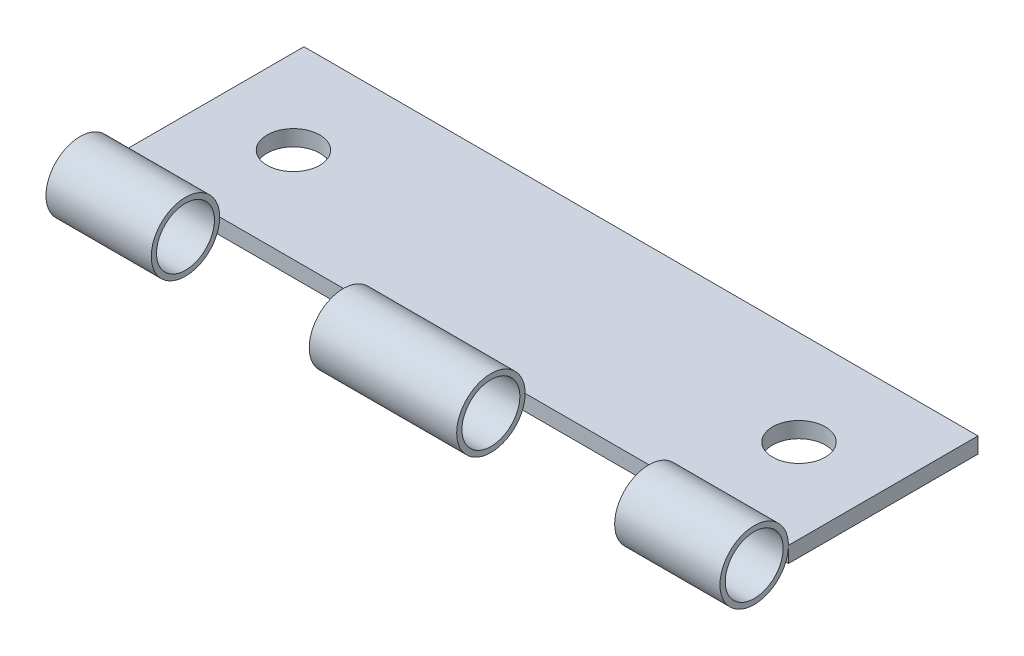
SolidWorks part; units mm, degrees
ref_plane "Front Plane" through (0, 0, 0) normal (0, 0, 1) x (1, 0, 0)
ref_plane "Top Plane" through (0, 0, 0) normal (0, 1, 0) x (1, 0, 0)
ref_plane "Right Plane" through (0, 0, 0) normal (1, 0, 0) x (0, 0, -1)
sketch "Sketch1" plane through (0, 0, 0) normal (0, 1, 0) x (1, 0, 0)
  line L1 (-32, 9) -> (32, 9)
  line L2 (-32, 9) -> (-32, -9)
  line L3 (-32, -9) -> (32, -9)
  line L4 (32, 9) -> (32, -9)
  line L5 (-32, 9) -> (32, -9) construction
  line L6 (-32, -9) -> (32, 9) construction
  point P0 (0, 0)
  dimension "D1" = 64
  dimension "D2" = 18
extrude "Boss-Extrude1" add sketch "Sketch1" along normal blind 1.5
sketch "Sketch2" plane through (0, 0, 0) normal (1, 0, 0) x (0, 0, -1)
  line L0 (-9, 1.5) -> (9, 1.5) construction
  line L1 (-9, 1.5) -> (-9, 0) construction
  circle A0 centre (-12.25, 1.5) radius 3.25
  dimension "D1" = 6.5
  dimension "D2" = 0
  dimension "D3" = 3.25
extrude "Boss-Extrude2" add sketch "Sketch2" along normal mid plane 64 separate body
sketch "Sketch3" plane through (0, 1.5, 0) normal (0, 1, 0) x (1, 0, 0)
  line L0 (-32, 9) -> (-32, -9) construction
  line L1 (32, -9) -> (32, 9) construction
  circle A0 centre (-24, 0) radius 2.5
  circle A1 centre (24, 0) radius 2.5
  dimension "D1" = 5
  dimension "D2" = 8
  dimension "D3" = 8
extrude "Cut-Extrude1" cut sketch "Sketch3" against normal blind 10
sketch "Sketch4" plane through (0, 0, 0) normal (0, 1, 0) x (1, 0, 0)
  line L34 (32, -9) -> (-32, -9) construction
  line L35 (-22, -9) -> (-7, -9)
  line L36 (-22, -9) -> (-22, -15.5)
  line L37 (-22, -15.5) -> (-7, -15.5)
  line L38 (-7, -9) -> (-7, -15.5)
  line L39 (-32, -15.5) -> (32, -15.5) construction
  line L40 (-32, -9) -> (-32, -15.5) construction
  line L41 (7, -9) -> (22, -9)
  line L42 (7, -9) -> (7, -15.5)
  line L43 (7, -15.5) -> (22, -15.5)
  line L44 (22, -9) -> (22, -15.5)
  line L45 (32, -15.5) -> (32, -9) construction
  dimension "D1" = 10
  dimension "D2" = 10
  dimension "D3" = 15
  dimension "D4" = 15
extrude "Cut-Extrude4" cut sketch "Sketch4" against normal blind 44 and the other way blind 44
sketch "Sketch6" plane through (32, 0, 0) normal (1, 0, 0) x (0, 0, -1)
  circle A0 centre (-12.25, 1.5) radius 2.75
  circle A1 centre (-12.25, 1.5) radius 3.25 construction
  dimension "D1" = 0.5
extrude "Cut-Extrude5" cut sketch "Sketch6" against normal blind 64
